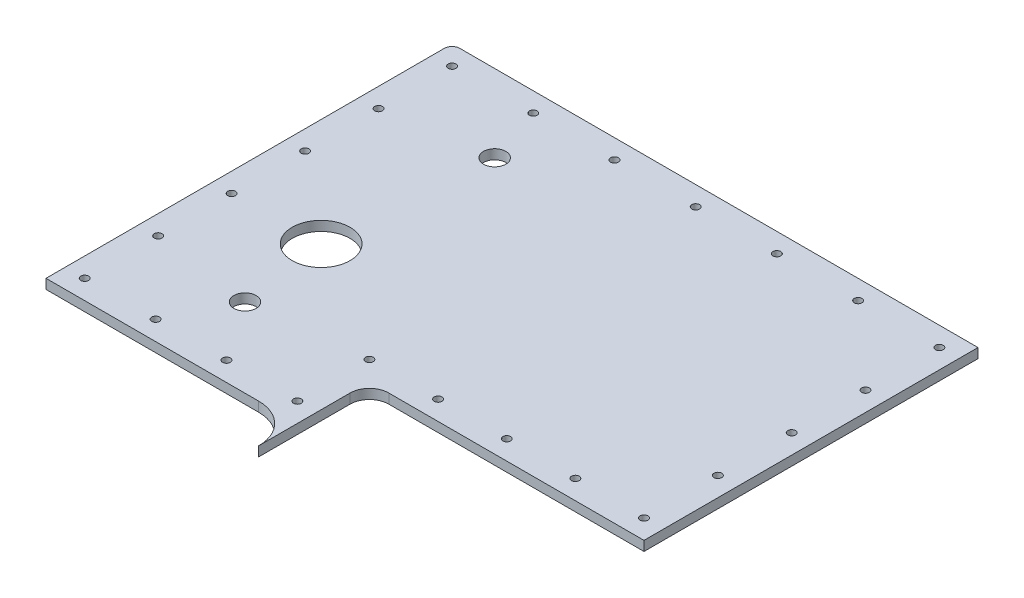
SolidWorks part; units mm, degrees
ref_plane "Front Plane" through (0, 0, 0) normal (0, 0, 1) x (1, 0, 0)
ref_plane "Top Plane" through (0, 0, 0) normal (0, 1, 0) x (1, 0, 0)
ref_plane "Right Plane" through (0, 0, 0) normal (1, 0, 0) x (0, 0, -1)
other "Bounding Box"
ref_plane "Default Plane" through (-8.9266, -12.7485, 0) normal (-0.1736, 0.9848, 0) x (0.9848, 0.1736, 0)
sketch "Sketch1" plane through (0, 0, 0) normal (0, 1, 0) x (1, 0, 0)
  line B0 (-8.89, -66.675) -> (-43.815, -66.675)
  line B1 (-43.815, -66.675) -> (-43.815, -1.27)
  line B2 (-42.545, 0) -> (42.545, 0)
  line B3 (42.545, 0) -> (42.545, -54.8431)
  line B4 (42.545, -54.8431) -> (-2.54, -54.8431)
  line B5 (-2.54, -54.8431) -> (-2.54, -73.025)
  arc B6 (-2.54, -73.025) -> (-8.89, -66.675) centre (-8.89, -73.025) ccw
  arc B7 (-42.545, 0) -> (-43.815, -1.27) centre (-42.545, -1.27) ccw
sketch_block_instance "Right Side sketch block-1"
sketch_block "Right Side sketch block"
extrude "Boss-Extrude1" add sketch "Sketch1" along normal blind 1.5875
fillet "Fillet1" radius 3.175 1 edges at (-2.54, 0.7937, 54.8431)
sketch "Sketch2" plane through (0, 1.5875, 0) normal (0, 1, 0) x (-1, 0, 0)
  line L0 (43.815, 1.27) -> (43.815, 66.675) construction
  line L1 (-42.545, 0) -> (42.545, 0) construction
  circle A0 centre (26.115, 39.2003) radius 4.75
  circle A1 centre (24.115, 53.7004) radius 1.83
  circle A2 centre (24.1149, 12.7) radius 1.83
  line B0 (21.0839, 10.9502) -> (17.115, 18.2002)
  line B1 (17.115, 18.2002) -> (17.115, 48.2004)
  line B2 (17.115, 48.2004) -> (21.0839, 55.4504)
  line B3 (31.115, 48.2004) -> (27.1461, 55.4504)
  line B4 (31.115, 48.2004) -> (31.115, 18.2002)
  line B5 (31.115, 18.2002) -> (27.1461, 10.9502)
  circle B6 centre (24.1149, 12.7) radius 1.83
  circle B7 centre (24.115, 53.7004) radius 1.83
  circle B8 centre (26.115, 39.2003) radius 4.75
  arc B9 (21.0839, 10.9502) -> (27.1461, 10.9502) centre (24.115, 12.7002) ccw
  arc B10 (27.1461, 55.4504) -> (21.0839, 55.4504) centre (24.115, 53.7005) ccw
  dimension "D1" = 12.7
  dimension "D2" = 12.7
sketch_block_instance "Switch+PD+Bord+V1-1"
sketch_block "Switch+PD+Bord+V1" parameters "D1"=9.5001, "D2"=3.66, "D3"=3.5
extrude "Cut-Extrude1" cut sketch "Sketch2" against normal through all both and the other way through all contours A0 | A1 | A2
sketch "Sketch3" plane through (0, 1.5875, 0) normal (0, 1, 0) x (-1, 0, 0)
  line L0 (-39.37, 3.175) -> (-39.37, 51.6681) construction
  line L1 (-39.37, 51.6681) -> (5.715, 51.6681) construction
  line L2 (5.715, 51.6681) -> (5.715, 63.5) construction
  line L3 (5.715, 63.5) -> (40.64, 63.5) construction
  line L4 (40.64, 63.5) -> (40.64, 3.175) construction
  line L5 (40.64, 3.175) -> (-39.37, 3.175) construction
  line L6 (-42.545, 0) -> (42.545, 0) construction
  line L7 (43.815, 1.27) -> (43.815, 66.675) construction
  line L8 (43.815, 66.675) -> (8.89, 66.675) construction
  line L9 (2.54, 73.025) -> (2.54, 58.0181) construction
  line L10 (-0.635, 54.8431) -> (-42.545, 54.8431) construction
  line L11 (-42.545, 54.8431) -> (-42.545, 0) construction
  circle A1 centre (27.305, 3.175) radius 0.635
  circle A2 centre (13.97, 3.175) radius 0.635
  circle A3 centre (0.635, 3.175) radius 0.635
  circle A4 centre (-12.7, 3.175) radius 0.635
  circle A5 centre (-26.035, 3.175) radius 0.635
  circle A6 centre (-39.37, 3.175) radius 0.635
  circle A7 centre (-39.37, 15.2983) radius 0.635
  circle A8 centre (-39.37, 27.4215) radius 0.635
  circle A9 centre (-39.37, 39.5448) radius 0.635
  circle A10 centre (-39.37, 51.6681) radius 0.635
  circle A11 centre (-28.0987, 51.6681) radius 0.635
  circle A12 centre (-16.8275, 51.6681) radius 0.635
  circle A13 centre (-5.5562, 51.6681) radius 0.635
  circle A14 centre (5.715, 51.6681) radius 0.635
  circle A15 centre (5.715, 63.5) radius 0.635
  circle A16 centre (17.3567, 63.5) radius 0.635
  circle A17 centre (28.9983, 63.5) radius 0.635
  circle A18 centre (40.64, 63.5) radius 0.635
  circle A19 centre (40.64, 51.435) radius 0.635
  circle A20 centre (40.64, 39.37) radius 0.635
  circle A21 centre (40.64, 27.305) radius 0.635
  circle A22 centre (40.64, 15.24) radius 0.635
  circle A24 centre (40.64, 3.175) radius 0.635 [skipped]
  circle A25 centre (40.64, 3.175) radius 0.635
  point P33 (0, 0)
  dimension "D7" = 1.27
  dimension "D14" = 13.335
  dimension "D15" = 13.335
  dimension "D18" = 13.335
  dimension "D1" = 3.175
  dimension "D2" = 3.175
  dimension "D3" = 3.175
  dimension "D4" = 3.175
  dimension "D5" = 3.175
  dimension "D6" = 3.175
  dimension "D8" = 12.065
  dimension "D16" = 13.335
  dimension "D17" = 13.335
  dimension "D9" = 5
  dimension "D10" = 5
  dimension "D11" = 2
  dimension "D12" = 4
  dimension "D13" = 6
extrude "Cut-Extrude2" cut sketch "Sketch3" against normal through all both and the other way through all
